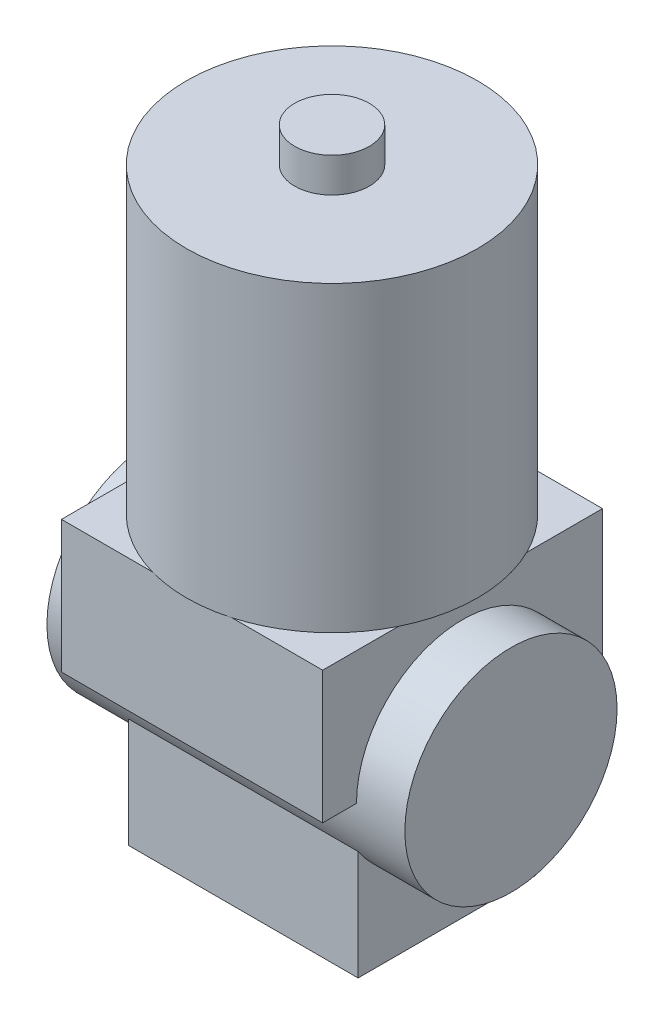
SolidWorks part; units mm, degrees
ref_plane "Front Plane" through (0, 0, 0) normal (0, 0, 1) x (1, 0, 0)
ref_plane "Top Plane" through (0, 0, 0) normal (0, 1, 0) x (1, 0, 0)
ref_plane "Right Plane" through (0, 0, 0) normal (1, 0, 0) x (0, 0, -1)
sketch "Sketch1" plane through (0, 0, 0) normal (0, 1, 0) x (1, 0, 0)
  circle A0 centre (0, 0) radius 15.595
  dimension "D1" = 31.19
extrude "Boss-Extrude1" add sketch "Sketch1" along normal blind 32.43
sketch "Sketch2" plane through (0, 32.43, 0) normal (0, 1, 0) x (1, 0, 0)
  circle A0 centre (0, 0) radius 4
  dimension "D1" = 8
extrude "Boss-Extrude2" add sketch "Sketch2" along normal blind 3.7
sketch "Sketch3" plane through (0, 0, 0) normal (0, -1, 0) x (1, 0, 0)
  line L1 (-14, -15) -> (14, -15)
  line L2 (-14, -15) -> (-14, 15)
  line L3 (-14, 15) -> (14, 15)
  line L4 (14, -15) -> (14, 15)
  line L5 (-14, -15) -> (14, 15) construction
  line L6 (-14, 15) -> (14, -15) construction
  point P0 (0, 0)
  dimension "D1" = 28
  dimension "D2" = 30
extrude "Boss-Extrude3" add sketch "Sketch3" along normal blind 14.18
ref_plane "Plane1" through (0, 0, 0) normal (-1, 0, 0) x (0, 0, 1)
sketch "Sketch5" plane through (0, 0, 0) normal (-1, 0, 0) x (0, 0, 1)
  line L0 (15, -14.18) -> (-15, -14.18) construction
  circle A0 centre (0, -14.18) radius 11.375
  dimension "D1" = 22.75
extrude "Boss-Extrude4" add sketch "Sketch5" along normal blind 19.185 and the other way blind 19.185
sketch "Sketch7" plane through (0, -14.18, 0) normal (0, -1, 0) x (1, 0, 0)
  line L0 (-19.185, 11.375) -> (19.185, -11.375) construction
  line L2 (-12.3, -9.5) -> (12.3, -9.5)
  line L3 (-12.3, -9.5) -> (-12.3, 9.5)
  line L4 (-12.3, 9.5) -> (12.3, 9.5)
  line L5 (12.3, -9.5) -> (12.3, 9.5)
  line L6 (-12.3, -9.5) -> (12.3, 9.5) construction
  line L7 (-12.3, 9.5) -> (12.3, -9.5) construction
  point P4 (0, 0)
  dimension "D1" = 24.6
  dimension "D2" = 19
extrude "Boss-Extrude5" add sketch "Sketch7" along normal blind 18
sketch "Sketch8" plane through (0, -32.18, 0) normal (0, -1, 0) x (1, 0, 0)
  line L0 (0, 7.799) -> (0, -7.799) construction
  line L1 (-12.3, 0) -> (12.3, 0) construction
  line L2 (-12.3, 9.5) -> (-12.3, -9.5) construction
  line L3 (12.3, -9.5) -> (12.3, 9.5) construction
  circle A0 centre (0, 5.595) radius 1.7419
  circle A1 centre (0, -5.595) radius 1.7419
  dimension "D1" = 11.19
extrude "Cut-Extrude1" cut sketch "Sketch8" against normal up to surface (18 mm away) up to face at (0, -14.18, 13.1875)
